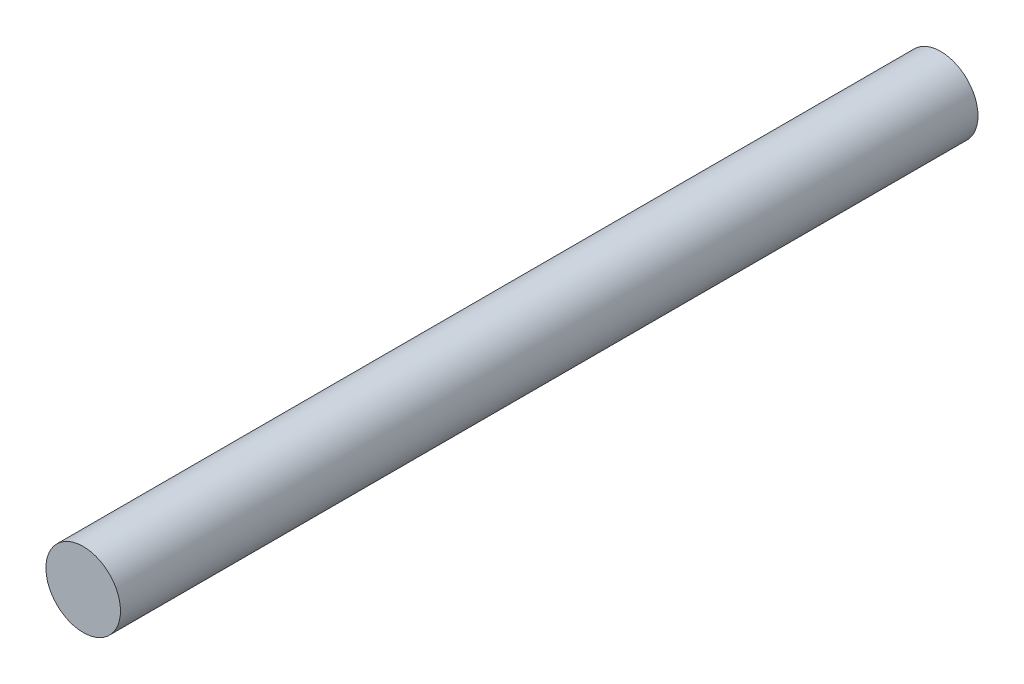
SolidWorks part; units mm, degrees
ref_plane "Front Plane" through (0, 0, 0) normal (0, 0, 1) x (1, 0, 0)
ref_plane "Top Plane" through (0, 0, 0) normal (0, 1, 0) x (1, 0, 0)
ref_plane "Right Plane" through (0, 0, 0) normal (1, 0, 0) x (0, 0, -1)
sketch "Sketch1" plane through (0, 0, 0) normal (0, 0, 1) x (1, 0, 0)
  circle A0 centre (0, 0) radius 4
  dimension "D1" = 8
extrude "Boss-Extrude1" add sketch "Sketch1" along normal blind 92
